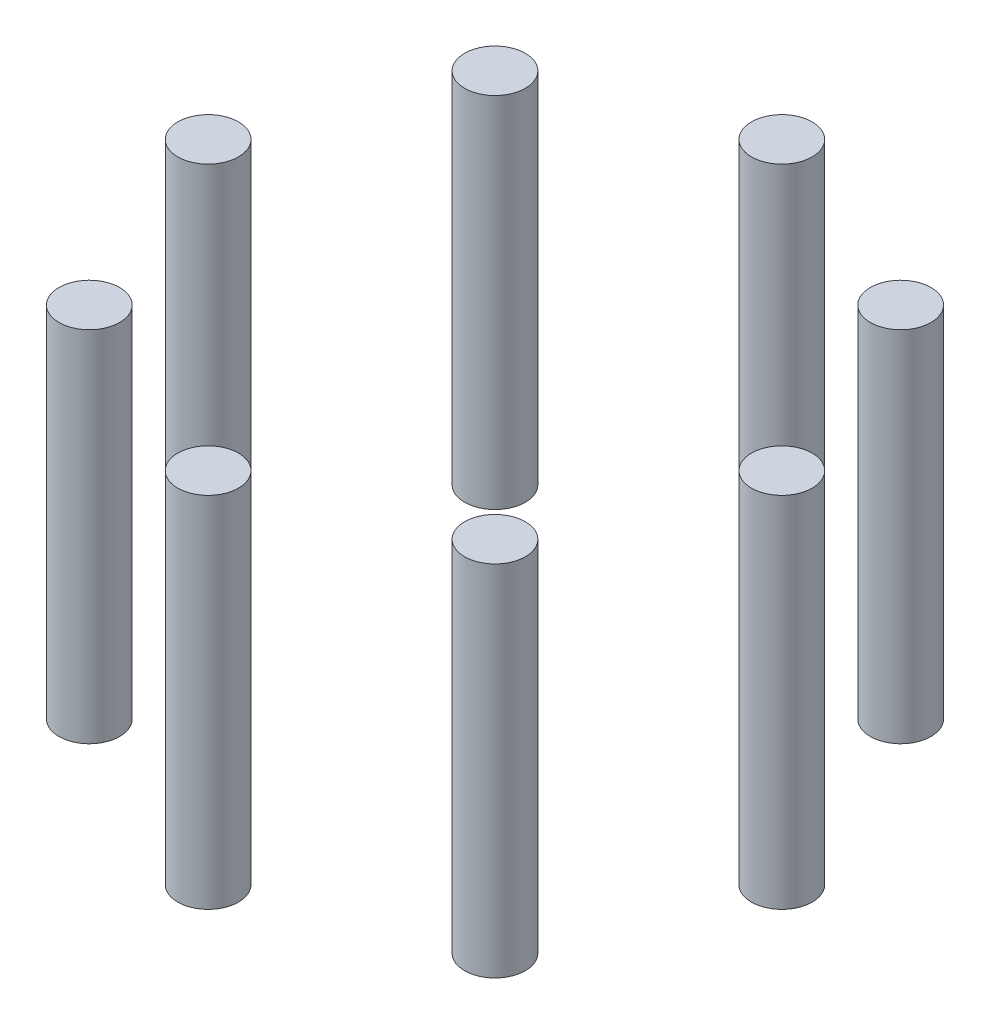
SolidWorks part; units mm, degrees
ref_plane "Front Plane" through (0, 0, 0) normal (0, 0, 1) x (1, 0, 0)
ref_plane "Top Plane" through (0, 0, 0) normal (0, 1, 0) x (1, 0, 0)
ref_plane "Right Plane" through (0, 0, 0) normal (1, 0, 0) x (0, 0, -1)
sketch "Sketch1" plane through (0, 0, 0) normal (0, 1, 0) x (1, 0, 0)
  circle A0 centre (0, 0) radius 52
  circle A1 centre (-52, 0) radius 5.5
  circle A2 centre (-36.7696, 36.7696) radius 5.5
  circle A3 centre (0, 52) radius 5.5
  circle A4 centre (36.7696, 36.7696) radius 5.5
  circle A5 centre (52, 0) radius 5.5
  circle A6 centre (36.7696, -36.7696) radius 5.5
  circle A7 centre (0, -52) radius 5.5
  circle A8 centre (-36.7696, -36.7696) radius 5.5
  point P21 (0, 0)
  dimension "D1" = 8
extrude "Boss-Extrude1" add sketch "Sketch1" along normal blind 65 contours A1 | A8 | A2 | A3 | A4 | A5 | A6 | A7
